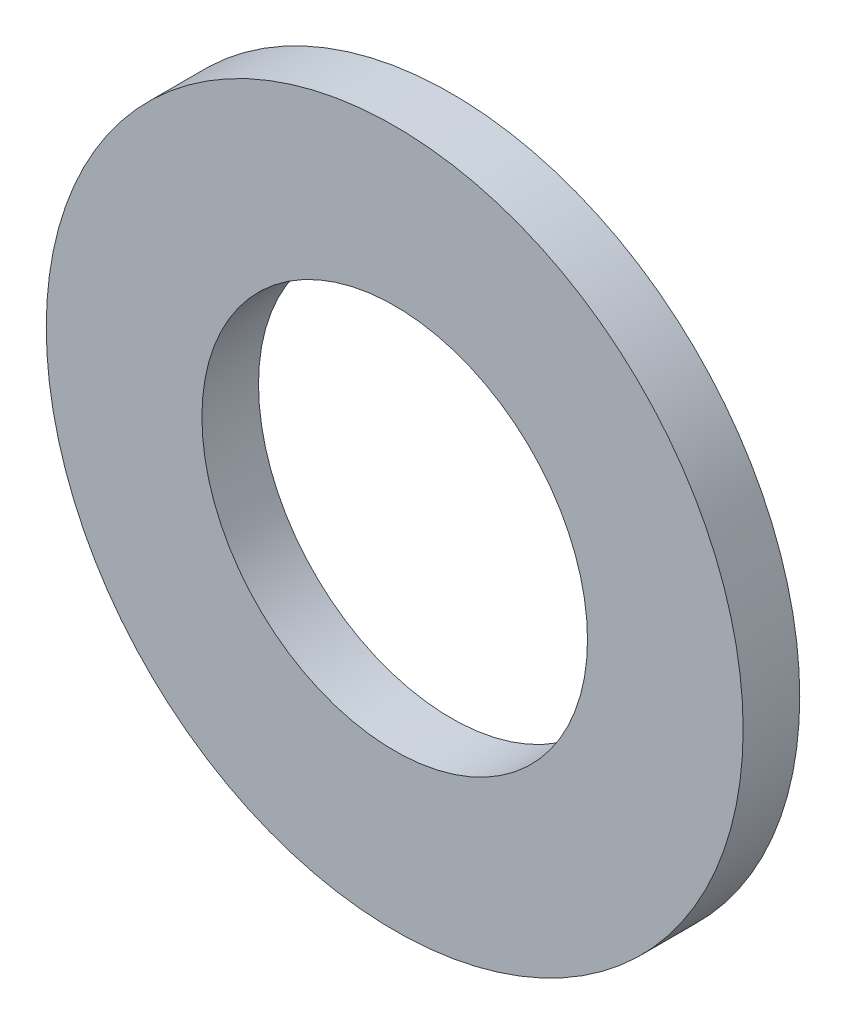
SolidWorks part; units mm, degrees
ref_plane "Front Plane" through (0, 0, 0) normal (0, 0, 1) x (1, 0, 0)
ref_plane "Top Plane" through (0, 0, 0) normal (0, 1, 0) x (1, 0, 0)
ref_plane "Right Plane" through (0, 0, 0) normal (1, 0, 0) x (0, 0, -1)
sketch "Sketch1" plane through (0, 0, 0) normal (0, 0, 1) x (1, 0, 0)
  circle A0 centre (0, 0) radius 9.85
  circle A1 centre (0, 0) radius 5.45
  dimension "OD" = 19.7
  dimension "ID" = 10.9
sketch "Sketch2" plane through (0, 0, 0) normal (1, 0, 0) x (0, 0, -1)
  line L0 (-0.8, -9.85) -> (0.8, -9.85)
  point P2 (0, -9.85)
sketch "Sketch3" plane through (0, 0, 0) normal (0, 0, 1) x (1, 0, 0)
  circle A0 centre (0, 0) radius 9.85 construction
  circle A1 centre (0, 0) radius 5.45 construction
  circle A2 centre (0, 0) radius 9.85
  circle A3 centre (0, 0) radius 5.45
extrude "Boss-Extrude1" add sketch "Sketch3" along normal mid plane 1.6
equation "\"D1@Boss-Extrude1\"=\"thickness@sketch2\""
